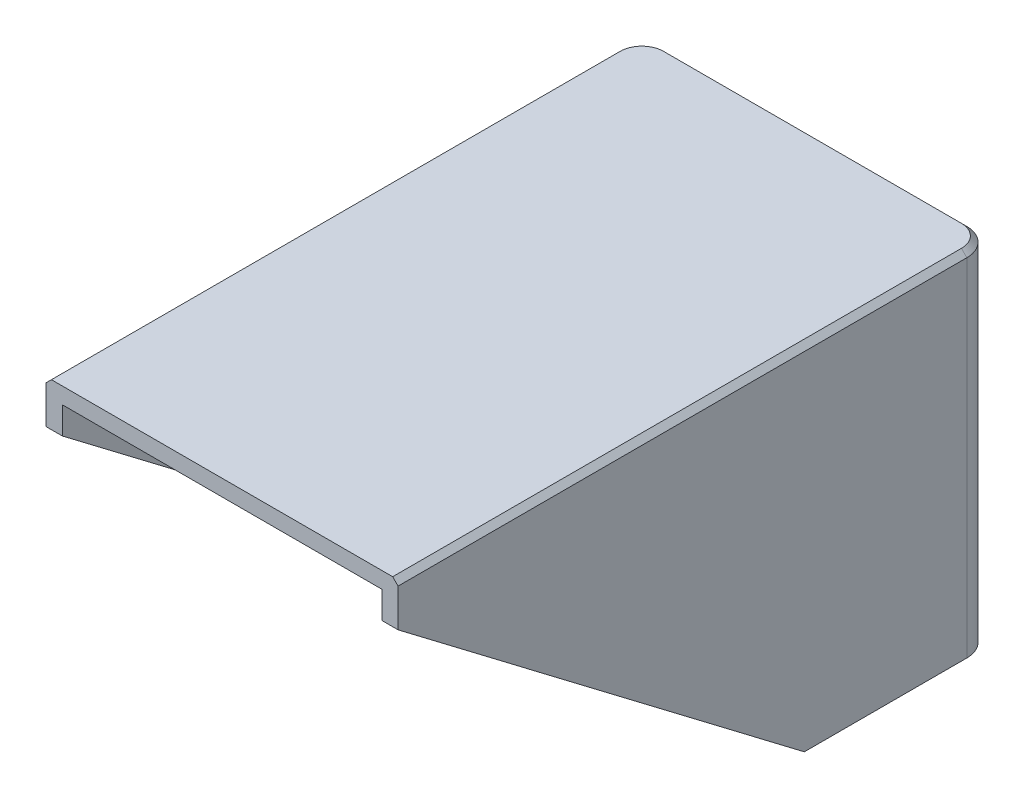
SolidWorks part; units mm, degrees
ref_plane "Plan de face" through (0, 0, 0) normal (0, 0, 1) x (1, 0, 0)
ref_plane "Plan de dessus" through (0, 0, 0) normal (0, 1, 0) x (1, 0, 0)
ref_plane "Plan de droite" through (0, 0, 0) normal (1, 0, 0) x (0, 0, -1)
sketch "Esquisse1" plane through (0, 0, 0) normal (0, 1, 0) x (1, 0, 0)
  line L1 (-32.5, -62.5) -> (32.5, -62.5)
  line L2 (-32.5, -62.5) -> (-32.5, 62.5)
  line L3 (-32.5, 62.5) -> (32.5, 62.5)
  line L4 (32.5, -62.5) -> (32.5, 62.5)
  line L5 (-32.5, -62.5) -> (32.5, 62.5) construction
  line L6 (-32.5, 62.5) -> (32.5, -62.5) construction
  point P0 (0, 0)
  dimension "D1" = 125
  dimension "D2" = 65
extrude "Boss.-Extru.1" add sketch "Esquisse1" along normal blind 80
shell "Coque1" thickness 3
sketch "Esquisse2" plane through (32.5, 0, 0) normal (1, 0, 0) x (0, 0, -1)
  line L0 (-47.5, 80) -> (-47.5, 72)
  line L1 (-62.5, 80) -> (62.5, 80) construction
  line L2 (-47.5, 72) -> (27.5, 15)
  line L3 (27.5, 15) -> (62.5, 15)
  line L4 (62.5, 80) -> (62.5, 0) construction
  line L5 (62.5, 15) -> (62.5, 80)
  line L6 (62.5, 80) -> (-47.5, 80)
  line L7 (-62.5, 80) -> (-62.5, 0) construction
  line L8 (-62.5, 0) -> (62.5, 0) construction
  dimension "D1" = 15
  dimension "D2" = 15
  dimension "D3" = 35
  dimension "D4" = 8
extrude "Enlèv. mat.-Extru.1" cut sketch "Esquisse2" against normal through all flip side to cut
fillet "Congé2" radius 5 2 edges at (-32.5, 47.5, -62.5) (32.5, 47.5, -62.5)
fillet "Congé3" radius 2 2 edges at (29.5, 46, -59.5) (-29.5, 46, -59.5)
chamfer "Chanfrein1" distance 1 angle 45 5 edges at (-32.5, 80, -5) (-31.0355, 80, -61.0355) (32.5, 80, -5) (0, 80, -62.5) (31.0355, 80, -61.0355)
sketch "Esquisse3" plane through (0, 0, -62.5) normal (0, 0, -1) x (-1, 0, 0)
  line L0 (27.5, 15) -> (-27.5, 15) construction
  line L1 (31.5, 80) -> (-31.5, 80) construction
  circle A0 centre (0, 55) radius 15.24
  point P5 (0, 15)
  dimension "D1" = 30.48
  dimension "D2" = 25
extrude "Enlèv. mat.-Extru.2" cut sketch "Esquisse3" against normal blind 0.1
